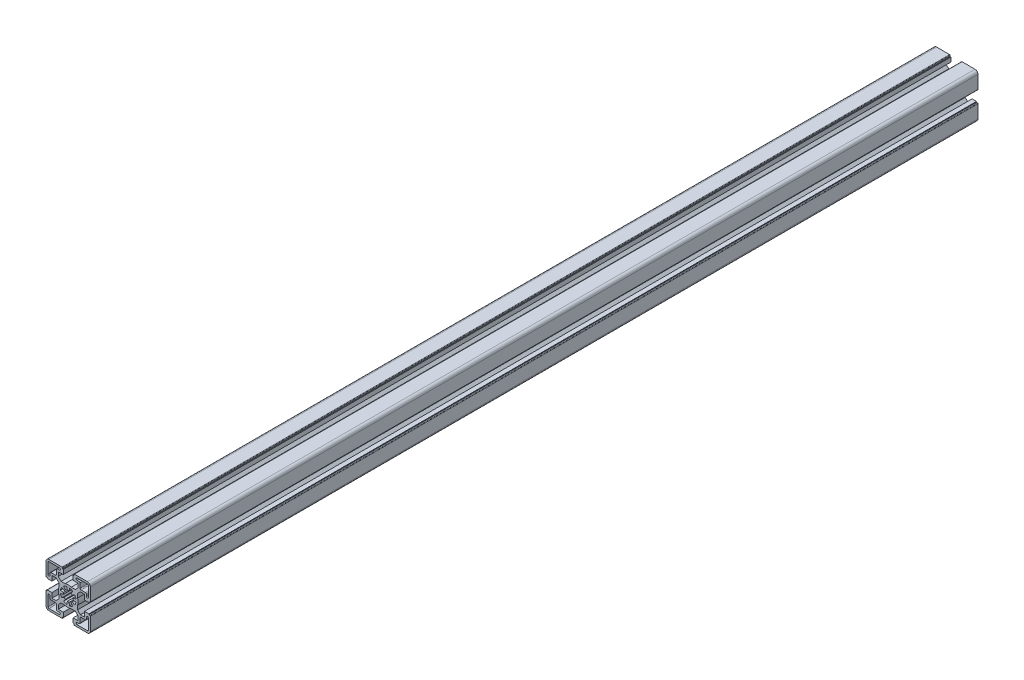
SolidWorks part; units mm, degrees
material "7079 Alloy"
ref_plane "Front Plane" through (0, 0, 0) normal (0, 0, 1) x (1, 0, 0)
ref_plane "Top Plane" through (0, 0, 0) normal (0, 1, 0) x (1, 0, 0)
ref_plane "Right Plane" through (0, 0, 0) normal (1, 0, 0) x (0, 0, -1)
sketch "Sketch1" plane through (0, 0, 0) normal (0, 0, 1) x (1, 0, 0)
  line L0 (0, 34.901) -> (0, -38.8683) construction
  line L1 (-27.7848, 0) -> (42.6814, 0) construction
  line L88 (0.8682, 4.924) -> (1.3892, 7.8784)
  line L89 (-0.8682, 4.924) -> (-1.3892, 7.8785)
  line L90 (-4.5886, 6.5532) -> (-2.8679, 4.0957)
  line L91 (-4.0957, 2.8679) -> (-6.5532, 4.5886)
  line L92 (-7.8784, 1.3892) -> (-4.924, 0.8682)
  line L93 (-7.8785, -1.3892) -> (-4.924, -0.8682)
  line L94 (-6.5532, -4.5886) -> (-4.0957, -2.8679)
  line L95 (-4.5886, -6.5532) -> (-2.8679, -4.0957)
  line L96 (-1.3892, -7.8784) -> (-0.8682, -4.924)
  line L97 (0.8682, -4.924) -> (1.3892, -7.8784)
  line L98 (4.5886, -6.5532) -> (2.8679, -4.0957)
  line L99 (4.0957, -2.8679) -> (6.5532, -4.5886)
  line L100 (7.8784, -1.3892) -> (4.924, -0.8682)
  line L101 (4.924, 0.8682) -> (7.8784, 1.3892)
  line L102 (4.0957, 2.8679) -> (6.5532, 4.5886)
  line L103 (2.8679, 4.0957) -> (4.5886, 6.5532)
  line L104 (-5, -16.4999) -> (-5, -20.9999)
  line L105 (-5, -20.9999) -> (-5.8, -20.9999)
  line L106 (-5.8, -20.9999) -> (-5.8, -22)
  line L107 (-6.3, -22.5) -> (-19.5, -22.5)
  line L108 (-22.5, -19.5) -> (-22.5, -6.2999)
  line L109 (-22, -5.7999) -> (-21, -5.7999)
  line L110 (-21, -5.7999) -> (-21, -4.9999)
  line L111 (-21, -4.9999) -> (-16.5, -4.9999)
  line L112 (-16.5, -4.9999) -> (-16.5, -10.0499)
  line L113 (-16.5, -10.0499) -> (-12.3429, -10.0499)
  line L114 (-12.3429, -10.0499) -> (-9.5, -7.207)
  line L115 (-9.5, -7.207) -> (-9.5, -3.1226)
  line L116 (-9.5, 3.1227) -> (-9.5, 7.207)
  line L117 (-9.5, 7.207) -> (-12.3429, 10.0499)
  line L118 (-12.3429, 10.0499) -> (-16.5, 10.0499)
  line L119 (-16.5, 10.0499) -> (-16.5, 4.9999)
  line L120 (-16.5, 4.9999) -> (-21, 4.9999)
  line L121 (-21, 4.9999) -> (-21, 5.7999)
  line L122 (-21, 5.7999) -> (-22, 5.7999)
  line L123 (-22.5, 6.2999) -> (-22.5, 19.5)
  line L124 (-19.5, 22.5) -> (-6.3, 22.5)
  line L125 (-5.7999, 21.9999) -> (-5.7999, 20.9999)
  line L126 (-5.7999, 20.9999) -> (-5, 20.9999)
  line L127 (-5, 20.9999) -> (-5, 16.5)
  line L128 (-5, 16.5) -> (-10.0501, 16.5)
  line L129 (-10.0501, 16.5) -> (-10.0501, 12.3428)
  line L130 (-10.0501, 12.3428) -> (-7.2072, 9.4999)
  line L131 (-7.2072, 9.4999) -> (-3.1228, 9.4999)
  line L132 (3.1226, 9.4999) -> (7.207, 9.4999)
  line L133 (7.207, 9.4999) -> (10.0499, 12.3428)
  line L134 (10.0499, 12.3428) -> (10.0499, 16.5)
  line L135 (10.0499, 16.5) -> (5, 16.5)
  line L136 (5, 16.5) -> (5, 21)
  line L137 (5, 21) -> (5.7999, 21)
  line L138 (5.7999, 21) -> (5.7999, 21.9999)
  line L139 (6.3, 22.5) -> (19.5001, 22.5)
  line L140 (22.5001, 6.2999) -> (22.5001, 19.5)
  line L141 (22.0001, 5.7999) -> (21, 5.7999)
  line L142 (21, 5.7999) -> (21, 4.9999)
  line L143 (21, 4.9999) -> (16.5, 4.9999)
  line L144 (16.5, 4.9999) -> (16.5, 10.0499)
  line L145 (16.5, 10.0499) -> (12.3429, 10.0499)
  line L146 (12.3429, 10.0499) -> (9.4999, 7.207)
  line L147 (9.4999, 7.207) -> (9.4999, 3.1227)
  line L148 (9.4999, -3.1226) -> (9.4999, -7.207)
  line L149 (9.4999, -7.207) -> (12.3429, -10.0499)
  line L150 (12.3429, -10.0499) -> (16.5, -10.0499)
  line L151 (16.5, -10.0499) -> (16.5, -4.9999)
  line L152 (16.5, -4.9999) -> (21, -4.9999)
  line L153 (21, -4.9999) -> (21, -5.7999)
  line L154 (21, -5.7999) -> (22.0001, -5.7999)
  line L155 (22.5001, -6.2999) -> (22.5001, -19.5)
  line L156 (6.3, -22.5) -> (19.5001, -22.5)
  line L157 (5.8, -22) -> (5.8, -20.9999)
  line L158 (5.8, -20.9999) -> (5, -20.9999)
  line L159 (5, -20.9999) -> (5, -16.4999)
  line L160 (5, -16.4999) -> (10.0499, -16.4999)
  line L161 (10.0499, -16.4999) -> (10.0499, -12.3428)
  line L162 (10.0499, -12.3428) -> (7.2069, -9.4998)
  line L163 (7.2069, -9.4998) -> (3.1226, -9.4998)
  line L164 (-3.1228, -9.4998) -> (-7.2071, -9.4998)
  line L165 (-7.2071, -9.4998) -> (-10.0501, -12.3428)
  line L166 (-10.0501, -12.3428) -> (-10.0501, -16.4999)
  line L167 (-10.0501, -16.4999) -> (-5, -16.4999)
  line L168 (-17.5001, -12) -> (-13.0001, -12)
  line L169 (-12.0001, -17.4999) -> (-12.0001, -13)
  line L170 (-11.0001, -18.4999) -> (-9.0001, -18.4999)
  line L171 (-19.5001, -20.5) -> (-9.0001, -20.5)
  line L172 (-20.5001, -19.5) -> (-20.5001, -8.9999)
  line L173 (-18.5001, -11) -> (-18.5001, -8.9999)
  line L174 (13, -12) -> (17.5, -12)
  line L175 (12, -17.4999) -> (12, -13)
  line L176 (9, -18.4999) -> (11, -18.4999)
  line L177 (9, -20.5) -> (19.5, -20.5)
  line L178 (20.5, -19.5) -> (20.5, -9.0001)
  line L179 (18.5, -11) -> (18.5, -9.0001)
  line L180 (-17.5001, 12) -> (-13.0001, 12)
  line L181 (-12.0001, 13) -> (-12.0001, 17.4999)
  line L182 (-11.0001, 18.4999) -> (-9.0001, 18.4999)
  line L183 (-19.5001, 20.5) -> (-9.0001, 20.5)
  line L184 (-20.5001, 8.9999) -> (-20.5001, 19.5)
  line L185 (-18.5001, 8.9999) -> (-18.5001, 11)
  line L186 (13, 12) -> (17.5, 12)
  line L187 (12, 13) -> (12, 17.4999)
  line L188 (9, 18.4999) -> (11, 18.4999)
  line L189 (9, 20.5) -> (19.5, 20.5)
  line L190 (20.5, 9.0001) -> (20.5, 19.5)
  line L191 (18.5, 9.0001) -> (18.5, 11)
  arc A56 (0.8682, 4.924) -> (-0.8682, 4.924) centre (0, 0) ccw
  arc A57 (-1.3892, 7.8785) -> (-4.5886, 6.5532) centre (0, 0) ccw
  arc A58 (-2.8679, 4.0957) -> (-4.0957, 2.8679) centre (0, 0) ccw
  arc A59 (-6.5532, 4.5886) -> (-7.8784, 1.3892) centre (0, 0) ccw
  arc A60 (-4.924, 0.8682) -> (-4.924, -0.8682) centre (0, 0) ccw
  arc A61 (-7.8785, -1.3892) -> (-6.5532, -4.5886) centre (0, 0) ccw
  arc A62 (-4.0957, -2.8679) -> (-2.8679, -4.0957) centre (0, 0) ccw
  arc A63 (-4.5886, -6.5532) -> (-1.3892, -7.8784) centre (0, 0) ccw
  arc A64 (-0.8682, -4.924) -> (0.8682, -4.924) centre (0, 0) ccw
  arc A65 (1.3892, -7.8784) -> (4.5886, -6.5532) centre (0, 0) ccw
  arc A66 (2.8679, -4.0957) -> (4.0957, -2.8679) centre (0, 0) ccw
  arc A67 (6.5532, -4.5886) -> (7.8784, -1.3892) centre (0, 0) ccw
  arc A68 (4.924, -0.8682) -> (4.924, 0.8682) centre (0, 0) ccw
  arc A69 (7.8784, 1.3892) -> (6.5532, 4.5886) centre (0, 0) ccw
  arc A70 (4.0957, 2.8679) -> (2.8679, 4.0957) centre (0, 0) ccw
  arc A71 (4.5886, 6.5532) -> (1.3892, 7.8784) centre (0, 0) ccw
  arc A72 (-6.3, -22.5) -> (-5.8, -22) centre (-6.3, -22) ccw
  arc A73 (-22.5, -19.5) -> (-19.5, -22.5) centre (-19.5, -19.5) ccw
  arc A74 (-22, -5.7999) -> (-22.5, -6.2999) centre (-22, -6.2999) ccw
  arc A75 (-9.5, 3.1227) -> (-9.5, -3.1226) centre (0, 0.0001) ccw
  arc A76 (-22.5, 6.2999) -> (-22, 5.7999) centre (-22, 6.2999) ccw
  arc A77 (-19.5, 22.5) -> (-22.5, 19.5) centre (-19.5, 19.5) ccw
  arc A78 (-5.7999, 21.9999) -> (-6.3, 22.5) centre (-6.3, 21.9999) ccw
  arc A79 (3.1226, 9.4999) -> (-3.1228, 9.4999) centre (-0.0001, -0.0001) ccw
  arc A80 (6.3, 22.5) -> (5.7999, 21.9999) centre (6.3, 21.9999) ccw
  arc A81 (22.5001, 19.5) -> (19.5001, 22.5) centre (19.5001, 19.5) ccw
  arc A82 (22.0001, 5.7999) -> (22.5001, 6.2999) centre (22.0001, 6.2999) ccw
  arc A83 (9.4999, -3.1226) -> (9.4999, 3.1227) centre (0, 0.0001) ccw
  arc A84 (22.5001, -6.2999) -> (22.0001, -5.7999) centre (22.0001, -6.2999) ccw
  arc A85 (19.5001, -22.5) -> (22.5001, -19.5) centre (19.5001, -19.5) ccw
  arc A86 (5.8, -22) -> (6.3, -22.5) centre (6.3, -22) ccw
  arc A87 (-3.1228, -9.4998) -> (3.1226, -9.4998) centre (-0.0001, 0.0001) ccw
  arc A88 (-18.5001, -11) -> (-17.5001, -12) centre (-17.5001, -11) ccw
  arc A89 (-12.0001, -13) -> (-13.0001, -12) centre (-13.0001, -13) ccw
  arc A90 (-12.0001, -17.4999) -> (-11.0001, -18.4999) centre (-11.0001, -17.4999) ccw
  arc A91 (-9.0001, -20.5) -> (-9.0001, -18.4999) centre (-9.0001, -19.5) ccw
  arc A92 (-20.5001, -19.5) -> (-19.5001, -20.5) centre (-19.5001, -19.5) ccw
  arc A93 (-18.5001, -8.9999) -> (-20.5001, -8.9999) centre (-19.5001, -8.9999) ccw
  arc A94 (17.5, -12) -> (18.5, -11) centre (17.5, -11) ccw
  arc A95 (13, -12) -> (12, -13) centre (13, -13) ccw
  arc A96 (11, -18.4999) -> (12, -17.4999) centre (11, -17.4999) ccw
  arc A97 (9, -18.4999) -> (9, -20.5) centre (9, -19.5) ccw
  arc A98 (19.5, -20.5) -> (20.5, -19.5) centre (19.5, -19.5) ccw
  arc A99 (20.5, -9.0001) -> (18.5, -9.0001) centre (19.5, -9.0001) ccw
  arc A100 (-17.5001, 12) -> (-18.5001, 11) centre (-17.5001, 11) ccw
  arc A101 (-13.0001, 12) -> (-12.0001, 13) centre (-13.0001, 13) ccw
  arc A102 (-11.0001, 18.4999) -> (-12.0001, 17.4999) centre (-11.0001, 17.4999) ccw
  arc A103 (-9.0001, 18.4999) -> (-9.0001, 20.5) centre (-9.0001, 19.5) ccw
  arc A104 (-19.5001, 20.5) -> (-20.5001, 19.5) centre (-19.5001, 19.5) ccw
  arc A105 (-20.5001, 8.9999) -> (-18.5001, 8.9999) centre (-19.5001, 8.9999) ccw
  arc A106 (18.5, 11) -> (17.5, 12) centre (17.5, 11) ccw
  arc A107 (12, 13) -> (13, 12) centre (13, 13) ccw
  arc A108 (12, 17.4999) -> (11, 18.4999) centre (11, 17.4999) ccw
  arc A109 (9, 20.5) -> (9, 18.4999) centre (9, 19.5) ccw
  arc A110 (20.5, 19.5) -> (19.5, 20.5) centre (19.5, 19.5) ccw
  arc A111 (18.5, 9.0001) -> (20.5, 9.0001) centre (19.5, 9.0001) ccw
  dimension "D5" = 10
  dimension "D1" = 45.0001
  dimension "D2" = 44.9999
  dimension "D3" = 12.5001
  dimension "D4" = 10
  dimension "D6" = 22.5001
extrude "Base-Extrude" add sketch "Sketch1" along normal blind 900
